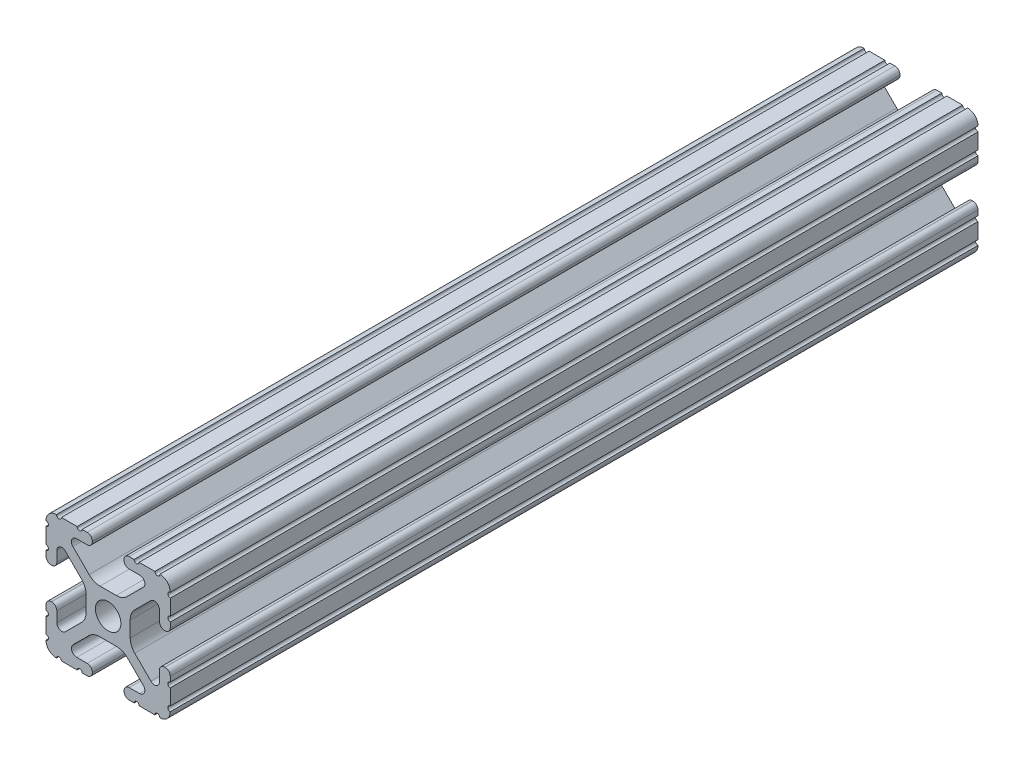
SolidWorks part; units mm, degrees
ref_plane "Front Plane" through (0, 0, 0) normal (0, 0, 1) x (1, 0, 0)
ref_plane "Top Plane" through (0, 0, 0) normal (0, 1, 0) x (1, 0, 0)
ref_plane "Right Plane" through (0, 0, 0) normal (1, 0, 0) x (0, 0, -1)
sketch "Sketch1" plane through (0, 0, 0) normal (0, 0, 1) x (1, 0, 0)
  line L88 (-7.1797, -8.6452) -> (-3.9523, -5.4237)
  line L89 (-1.7093, -4.4958) -> (1.7093, -4.4958)
  line L90 (3.9523, -5.4237) -> (7.1797, -8.6452)
  line L91 (6.4164, -10.4902) -> (4.2875, -10.4902)
  line L92 (3.2385, -11.5392) -> (3.2385, -11.651)
  line L93 (4.2875, -12.7) -> (5.3171, -12.7)
  line L94 (6.3331, -12.7) -> (9.5504, -12.7)
  line L95 (12.7, -9.5504) -> (12.7, -6.3331)
  line L96 (12.7, -5.3171) -> (12.7, -4.2875)
  line L97 (11.651, -3.2385) -> (11.5392, -3.2385)
  line L98 (10.4902, -4.2875) -> (10.4902, -6.4021)
  line L99 (8.7371, -7.1294) -> (5.441, -3.8408)
  line L100 (4.5085, -1.5932) -> (4.5085, 1.5932)
  line L101 (5.441, 3.8408) -> (8.7371, 7.1294)
  line L102 (10.4902, 6.4021) -> (10.4902, 4.2875)
  line L103 (11.5392, 3.2385) -> (11.651, 3.2385)
  line L104 (12.7, 4.2875) -> (12.7, 5.3171)
  line L105 (12.7, 6.3331) -> (12.7, 9.5504)
  line L106 (9.5504, 12.7) -> (6.3331, 12.7)
  line L107 (5.3171, 12.7) -> (4.2875, 12.7)
  line L108 (3.2385, 11.651) -> (3.2385, 11.5392)
  line L109 (4.2875, 10.4902) -> (6.4768, 10.4902)
  line L110 (7.207, 8.7244) -> (3.8983, 5.4232)
  line L111 (1.6558, 4.4958) -> (-1.6558, 4.4958)
  line L112 (-3.8983, 5.4232) -> (-7.207, 8.7244)
  line L113 (-6.4768, 10.4902) -> (-4.2875, 10.4902)
  line L114 (-3.2385, 11.5392) -> (-3.2385, 11.651)
  line L115 (-4.2875, 12.7) -> (-5.3171, 12.7)
  line L116 (-6.3331, 12.7) -> (-9.5504, 12.7)
  line L117 (-12.7, 9.5504) -> (-12.7, 6.3331)
  line L118 (-12.7, 5.3171) -> (-12.7, 4.2875)
  line L119 (-11.651, 3.2385) -> (-11.5392, 3.2385)
  line L120 (-10.4902, 4.2875) -> (-10.4902, 6.4021)
  line L121 (-8.7371, 7.1294) -> (-5.441, 3.8408)
  line L122 (-4.5085, 1.5932) -> (-4.5085, -1.5932)
  line L123 (-5.441, -3.8408) -> (-8.7371, -7.1294)
  line L124 (-10.4902, -6.4021) -> (-10.4902, -4.2875)
  line L125 (-11.5392, -3.2385) -> (-11.651, -3.2385)
  line L126 (-12.7, -4.2875) -> (-12.7, -5.3171)
  line L127 (-12.7, -6.3331) -> (-12.7, -9.5504)
  line L128 (-9.5504, -12.7) -> (-6.3331, -12.7)
  line L129 (-5.3171, -12.7) -> (-4.2875, -12.7)
  line L130 (-3.2385, -11.651) -> (-3.2385, -11.5392)
  line L131 (-4.2875, -10.4902) -> (-6.4164, -10.4902)
  circle A1 centre (0, 0) radius 2.6035
  arc A104 (-7.1797, -8.6452) -> (-6.4164, -10.4902) centre (-6.4164, -9.4098) ccw
  arc A105 (-1.7093, -4.4958) -> (-3.9523, -5.4237) centre (-1.7093, -7.6708) ccw
  arc A106 (3.9523, -5.4237) -> (1.7093, -4.4958) centre (1.7093, -7.6708) ccw
  arc A107 (6.4164, -10.4902) -> (7.1797, -8.6452) centre (6.4164, -9.4098) ccw
  arc A108 (4.2875, -10.4902) -> (3.2385, -11.5392) centre (4.2875, -11.5392) ccw
  arc A109 (3.2385, -11.651) -> (4.2875, -12.7) centre (4.2875, -11.651) ccw
  arc A110 (6.3331, -12.7) -> (5.3171, -12.7) centre (5.8251, -12.7) ccw
  arc A111 (10.5664, -12.6998) -> (9.5504, -12.7) centre (10.0584, -12.7) ccw
  arc A112 (10.5664, -12.6998) -> (12.6998, -10.5664) centre (10.5918, -10.5918) ccw
  arc A113 (12.7, -9.5504) -> (12.6998, -10.5664) centre (12.7, -10.0584) ccw
  arc A114 (12.7, -5.3171) -> (12.7, -6.3331) centre (12.7, -5.8251) ccw
  arc A115 (12.7, -4.2875) -> (11.651, -3.2385) centre (11.651, -4.2875) ccw
  arc A116 (11.5392, -3.2385) -> (10.4902, -4.2875) centre (11.5392, -4.2875) ccw
  arc A117 (8.7371, -7.1294) -> (10.4902, -6.4021) centre (9.4628, -6.4021) ccw
  arc A118 (4.5085, -1.5932) -> (5.441, -3.8408) centre (7.6835, -1.5932) ccw
  arc A119 (5.441, 3.8408) -> (4.5085, 1.5932) centre (7.6835, 1.5932) ccw
  arc A120 (10.4902, 6.4021) -> (8.7371, 7.1294) centre (9.4628, 6.4021) ccw
  arc A121 (10.4902, 4.2875) -> (11.5392, 3.2385) centre (11.5392, 4.2875) ccw
  arc A122 (11.651, 3.2385) -> (12.7, 4.2875) centre (11.651, 4.2875) ccw
  arc A123 (12.7, 6.3331) -> (12.7, 5.3171) centre (12.7, 5.8251) ccw
  arc A124 (12.6998, 10.5664) -> (12.7, 9.5504) centre (12.7, 10.0584) ccw
  arc A125 (12.6998, 10.5664) -> (10.5664, 12.6998) centre (10.5918, 10.5918) ccw
  arc A126 (9.5504, 12.7) -> (10.5664, 12.6998) centre (10.0584, 12.7) ccw
  arc A127 (5.3171, 12.7) -> (6.3331, 12.7) centre (5.8251, 12.7) ccw
  arc A128 (4.2875, 12.7) -> (3.2385, 11.651) centre (4.2875, 11.651) ccw
  arc A129 (3.2385, 11.5392) -> (4.2875, 10.4902) centre (4.2875, 11.5392) ccw
  arc A130 (7.207, 8.7244) -> (6.4768, 10.4902) centre (6.4768, 9.4563) ccw
  arc A131 (1.6558, 4.4958) -> (3.8983, 5.4232) centre (1.6558, 7.6708) ccw
  arc A132 (-3.8983, 5.4232) -> (-1.6558, 4.4958) centre (-1.6558, 7.6708) ccw
  arc A133 (-6.4768, 10.4902) -> (-7.207, 8.7244) centre (-6.4768, 9.4563) ccw
  arc A134 (-4.2875, 10.4902) -> (-3.2385, 11.5392) centre (-4.2875, 11.5392) ccw
  arc A135 (-3.2385, 11.651) -> (-4.2875, 12.7) centre (-4.2875, 11.651) ccw
  arc A136 (-6.3331, 12.7) -> (-5.3171, 12.7) centre (-5.8251, 12.7) ccw
  arc A137 (-10.5664, 12.6998) -> (-9.5504, 12.7) centre (-10.0584, 12.7) ccw
  arc A138 (-10.5664, 12.6998) -> (-12.6998, 10.5664) centre (-10.5918, 10.5918) ccw
  arc A139 (-12.7, 9.5504) -> (-12.6998, 10.5664) centre (-12.7, 10.0584) ccw
  arc A140 (-12.7, 5.3171) -> (-12.7, 6.3331) centre (-12.7, 5.8251) ccw
  arc A141 (-12.7, 4.2875) -> (-11.651, 3.2385) centre (-11.651, 4.2875) ccw
  arc A142 (-11.5392, 3.2385) -> (-10.4902, 4.2875) centre (-11.5392, 4.2875) ccw
  arc A143 (-8.7371, 7.1294) -> (-10.4902, 6.4021) centre (-9.4628, 6.4021) ccw
  arc A144 (-4.5085, 1.5932) -> (-5.441, 3.8408) centre (-7.6835, 1.5932) ccw
  arc A145 (-5.441, -3.8408) -> (-4.5085, -1.5932) centre (-7.6835, -1.5932) ccw
  arc A146 (-10.4902, -6.4021) -> (-8.7371, -7.1294) centre (-9.4628, -6.4021) ccw
  arc A147 (-10.4902, -4.2875) -> (-11.5392, -3.2385) centre (-11.5392, -4.2875) ccw
  arc A148 (-11.651, -3.2385) -> (-12.7, -4.2875) centre (-11.651, -4.2875) ccw
  arc A149 (-12.7, -6.3331) -> (-12.7, -5.3171) centre (-12.7, -5.8251) ccw
  arc A150 (-12.6998, -10.5664) -> (-12.7, -9.5504) centre (-12.7, -10.0584) ccw
  arc A151 (-12.6998, -10.5664) -> (-10.5664, -12.6998) centre (-10.5918, -10.5918) ccw
  arc A152 (-9.5504, -12.7) -> (-10.5664, -12.6998) centre (-10.0584, -12.7) ccw
  arc A153 (-5.3171, -12.7) -> (-6.3331, -12.7) centre (-5.8251, -12.7) ccw
  arc A154 (-4.2875, -12.7) -> (-3.2385, -11.651) centre (-4.2875, -11.651) ccw
  arc A155 (-3.2385, -11.5392) -> (-4.2875, -10.4902) centre (-4.2875, -11.5392) ccw
extrude "Boss-Extrude1" add sketch "Sketch1" along normal mid plane 165.1
